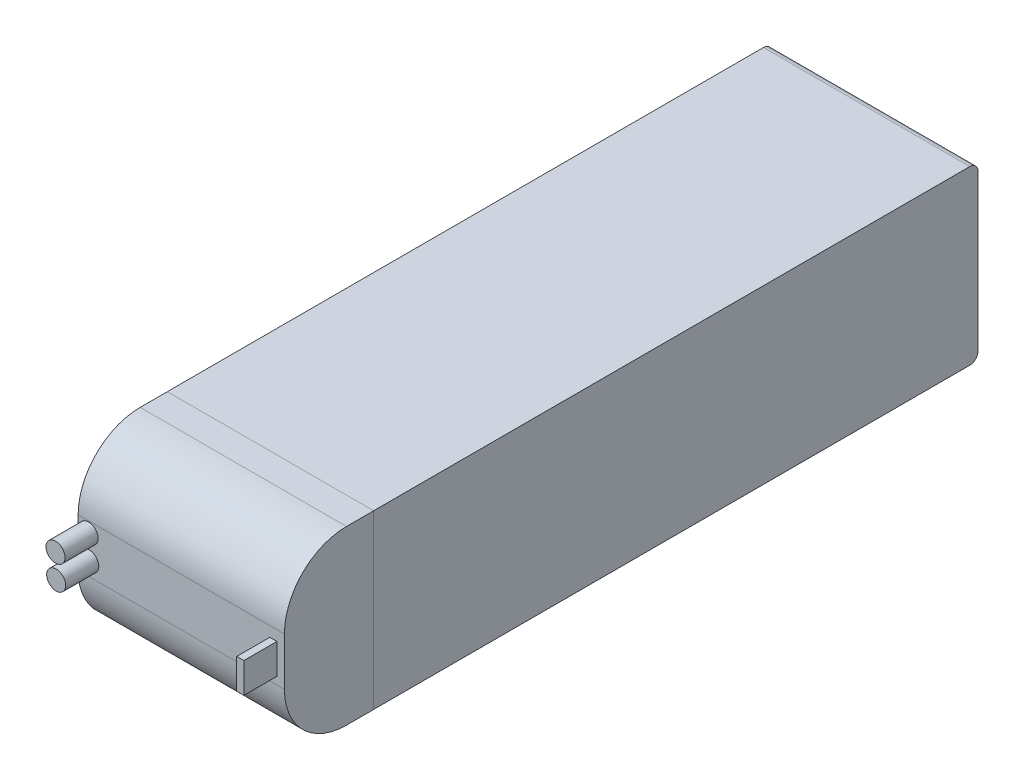
SolidWorks part; units mm, degrees
ref_plane "Front Plane" through (0, 0, 0) normal (0, 0, 1) x (1, 0, 0)
ref_plane "Top Plane" through (0, 0, 0) normal (0, 1, 0) x (1, 0, 0)
ref_plane "Right Plane" through (0, 0, 0) normal (1, 0, 0) x (0, 0, -1)
sketch "Sketch1" plane through (0, 0, 0) normal (0, 1, 0) x (1, 0, 0)
  line L1 (24.935, -73.055) -> (-24.935, -73.055)
  line L2 (24.935, -73.055) -> (24.935, 73.055)
  line L3 (24.935, 73.055) -> (-24.935, 73.055)
  line L4 (-24.935, -73.055) -> (-24.935, 73.055)
  line L5 (24.935, -73.055) -> (-24.935, 73.055) construction
  line L6 (24.935, 73.055) -> (-24.935, -73.055) construction
  point P0 (0, 0)
  dimension "D1" = 49.87
  dimension "D2" = 146.11
extrude "Boss-Extrude1" add sketch "Sketch1" along normal blind 41.6
sketch "Sketch2" plane through (0, 0, 73.055) normal (0, 0, 1) x (1, 0, 0)
  line L1 (24.9567, 0.0105) -> (-24.9133, 0.0105)
  line L2 (24.9567, 0.0105) -> (24.9567, 41.6105)
  line L3 (24.9567, 41.6105) -> (-24.9133, 41.6105)
  line L4 (-24.9133, 0.0105) -> (-24.9133, 41.6105)
  line L5 (24.9567, 0.0105) -> (-24.9133, 41.6105) construction
  line L6 (24.9567, 41.6105) -> (-24.9133, 0.0105) construction
  point P0 (0.0217, 20.8105)
  dimension "D1" = 49.87
  dimension "D2" = 41.6
extrude "Boss-Extrude2" add sketch "Sketch2" along normal blind 21.57
fillet "Fillet2" radius 15 2 edges at (0.0217, 0.0105, 94.625) (0.0217, 41.6105, 94.625)
sketch "Sketch6" plane through (0, 0, 94.625) normal (0, 0, 1) x (1, 0, 0)
  circle A0 centre (-22.3821, 24.0766) radius 2.305
  point P2 (-22.3821, 24.0766)
extrude "Boss-Extrude4" add sketch "Sketch6" along normal blind 8
sketch "Sketch7" plane through (0, 0, 94.625) normal (0, 0, 1) x (1, 0, 0)
  circle A0 centre (-22.2264, 18.3128) radius 2.305
  point P2 (-22.2264, 18.3128)
extrude "Boss-Extrude5" add sketch "Sketch7" along normal blind 8
sketch "Sketch8" plane through (0, 0, 94.625) normal (0, 0, 1) x (1, 0, 0)
  line L1 (21.427, 24.1437) -> (23.147, 24.1437)
  line L2 (21.427, 24.1437) -> (21.427, 16.8437)
  line L3 (21.427, 16.8437) -> (23.147, 16.8437)
  line L4 (23.147, 24.1437) -> (23.147, 16.8437)
  line L5 (21.427, 24.1437) -> (23.147, 16.8437) construction
  line L6 (21.427, 16.8437) -> (23.147, 24.1437) construction
  point P0 (22.287, 20.4937)
  point P5 (21.4692, 20.7663)
  point P6 (22.287, 20.4937)
  dimension "D1" = 1.72
  dimension "D2" = 7.3
extrude "Boss-Extrude6" add sketch "Sketch8" along normal blind 8
fillet "Fillet3" radius 2 2 edges at (0, 0, -73.055) (0, 41.6, -73.055)
sketch "Sketch4" plane through (0, 0, 94.625) normal (0, 0, 1) x (1, 0, 0)
  circle A0 centre (-10.6485, 20.5725) radius 2.305
  point P2 (-10.6485, 20.5725)
  point P3 (-32.9527, -9.0731)
  point P4 (0, 0)
  point P5 (0, 0)
  dimension "D1" = 4.61
